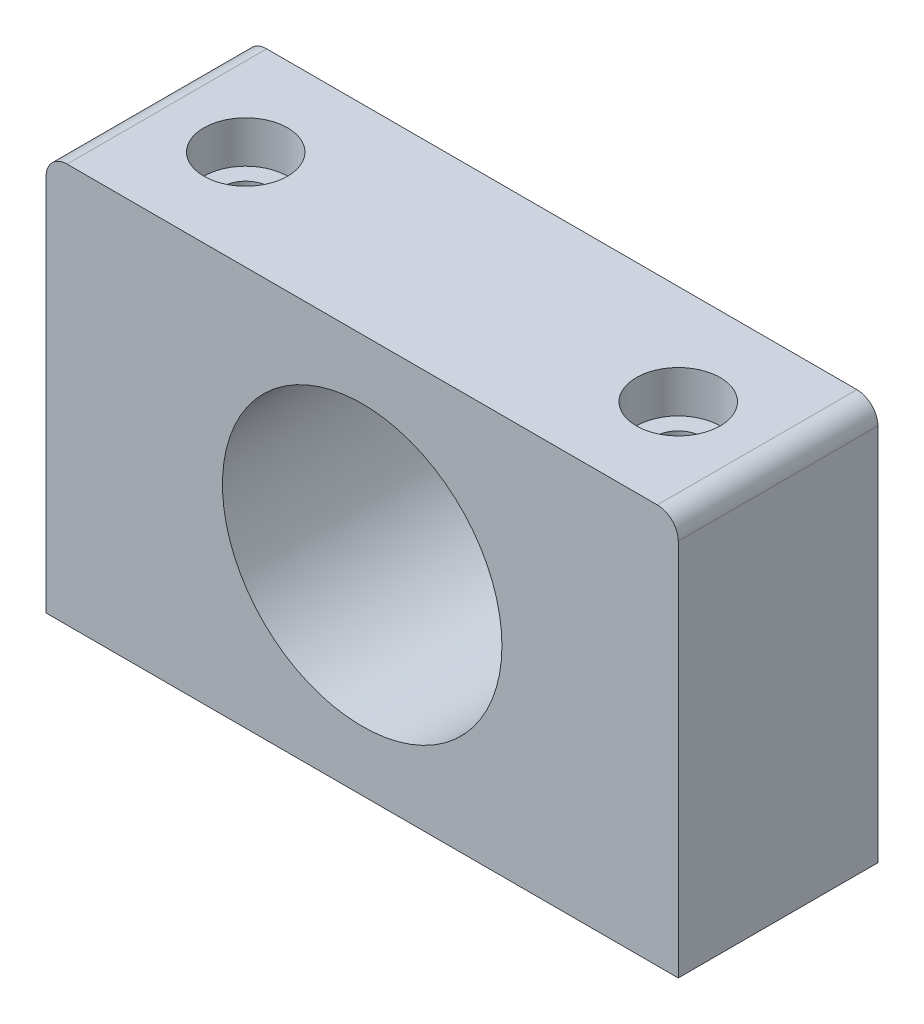
SolidWorks part; units mm, degrees
ref_plane "Front Plane" through (0, 0, 0) normal (0, 0, 1) x (1, 0, 0)
ref_plane "Top Plane" through (0, 0, 0) normal (0, 1, 0) x (1, 0, 0)
ref_plane "Right Plane" through (0, 0, 0) normal (1, 0, 0) x (0, 0, -1)
sketch "Sketch1" plane through (0, 0, 0) normal (0, 1, 0) x (1, 0, 0)
  line L1 (-30.1625, -9.525) -> (30.1625, -9.525)
  line L2 (-30.1625, -9.525) -> (-30.1625, 9.525)
  line L3 (-30.1625, 9.525) -> (30.1625, 9.525)
  line L4 (30.1625, -9.525) -> (30.1625, 9.525)
  line L5 (-30.1625, -9.525) -> (30.1625, 9.525) construction
  line L6 (-30.1625, 9.525) -> (30.1625, -9.525) construction
  point P0 (0, 0)
  dimension "D1" = 19.05
  dimension "D2" = 60.325
extrude "Boss-Extrude1" add sketch "Sketch1" along normal blind 38.1
sketch "Sketch2" plane through (0, 0, 9.525) normal (0, 0, 1) x (1, 0, 0)
  line L1 (-30.1625, 0) -> (30.1625, 0) construction
  circle A0 centre (0, 19.05) radius 13.335
  dimension "D1" = 26.67
  dimension "D2" = 19.05
extrude "Cut-Extrude1" cut sketch "Sketch2" against normal through all contours A0
sketch "Sketch4" plane through (0, 38.1, 0) normal (0, 1, 0) x (1, 0, 0)
  line L0 (0, 9.525) -> (0, -9.525) construction
  line L1 (30.1625, 9.525) -> (-30.1625, 9.525) construction
  line L2 (-30.1625, -9.525) -> (30.1625, -9.525) construction
  line L3 (-30.1625, 0) -> (30.1625, 0) construction
  line L4 (-30.1625, 9.525) -> (-30.1625, -9.525) construction
  line L5 (30.1625, -9.525) -> (30.1625, 9.525) construction
  point P0 (-20.6375, 0)
  point P1 (20.6375, 0)
  dimension "D1" = 41.275
hole_wizard "CBORE for M4 SHCS1" positions "Sketch5" profile "Sketch6" counterbore size "M4" standard "ANSI Metric" end condition through all
sketch "Sketch5" plane through (0, 38.1, 0) normal (0, 1, 0) x (1, 0, 0)
  point P0 (-20.6375, 0)
  point P3 (20.6375, 0)
sketch "Sketch6" plane through (-20.6375, 38.1, 0) normal (1, 0, 0) x (0, 0, 1)
  line L0 (0, 0) -> (0, 38.1)
  line L1 (0, 38.1) -> (2.25, 38.1)
  line L3 (2.25, 38.1) -> (2.25, 4)
  line L4 (2.25, 4) -> (4, 4)
  line L5 (4, 4) -> (4, 0)
  line L7 (4, 0) -> (0, 0)
  line L11 (0, -6.35) -> (0, 107.95) construction
  dimension "Thru Hole Dia." = 4.5
  dimension "Thru Hole Depth" = 38.1
  dimension "C'Bore Dia." = 8
  dimension "C'Bore Depth" = 4
fillet "Fillet1" radius 2 2 edges at (30.1625, 38.1, 0) (-30.1625, 38.1, 0)
